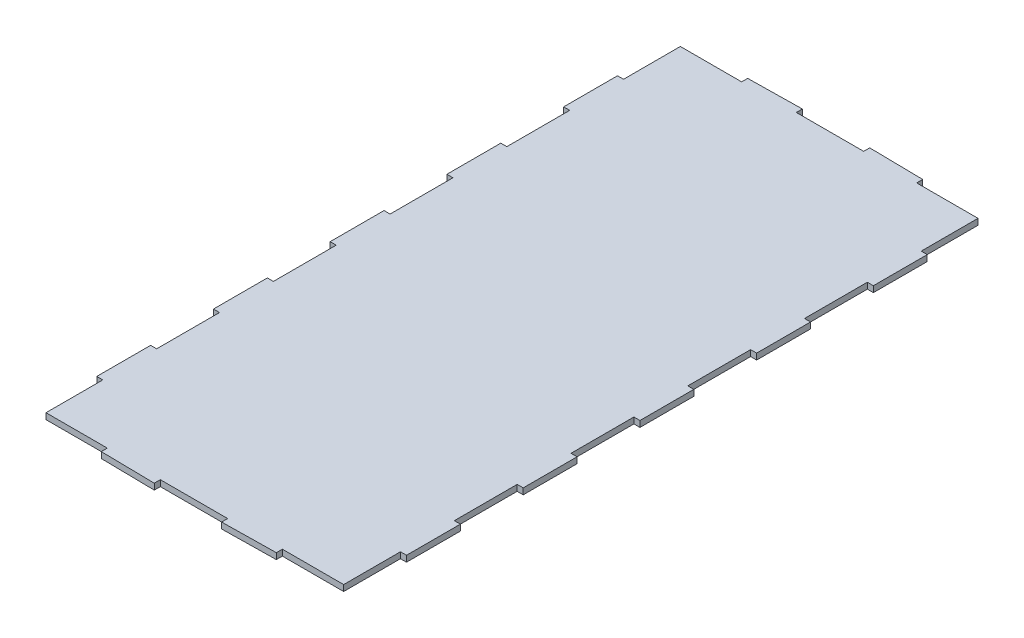
SolidWorks part; units mm, degrees
ref_plane "Front Plane" through (0, 0, 0) normal (0, 0, 1) x (1, 0, 0)
ref_plane "Top Plane" through (0, 0, 0) normal (0, 1, 0) x (1, 0, 0)
ref_plane "Right Plane" through (0, 0, 0) normal (1, 0, 0) x (0, 0, -1)
sketch "Sketch1" plane through (0, 0, 0) normal (0, 1, 0) x (1, 0, 0)
  line L0 (0, 0) -> (0, 299.8917) construction
  line L7 (0, 0) -> (146.05, 0) construction
  line L73 (31.75, 299.8917) -> (-31.75, 299.8917)
  line L102 (31.75, 305.5917) -> (31.75, 299.8917) construction
  line L103 (82.5438, 304.7999) -> (31.75, 305.5917) construction
  line L104 (82.55, 299.0999) -> (82.5438, 304.7999) construction
  line L107 (140.35, 245.5366) -> (146.05, 245.5366)
  line L109 (82.55, 299.0999) -> (82.5438, 304.7999)
  line L110 (82.5438, 304.7999) -> (31.75, 305.5917)
  line L111 (31.75, 305.5917) -> (31.75, 299.8917)
  line L123 (140.35, 245.5366) -> (140.35, 299.0999)
  line L129 (146.05, 245.5366) -> (146.05, 194.7366)
  line L130 (82.55, 299.0999) -> (140.35, 299.0999)
  line L154 (146.05, 194.7366) -> (140.35, 194.7366)
  line L156 (140.35, 194.7366) -> (140.35, 135.47)
  line L157 (140.35, 135.47) -> (146.05, 135.47)
  line L158 (146.05, 135.47) -> (146.05, 84.67)
  line L159 (146.05, 84.67) -> (140.35, 84.67)
  line L160 (140.35, 84.67) -> (140.35, 25.4)
  line L161 (140.35, 25.4) -> (146.05, 25.4)
  line L163 (146.05, 25.4) -> (146.05, -25.4)
  line L165 (-146.05, 25.4) -> (-146.05, -25.4)
  line L166 (-140.35, 245.5366) -> (-140.35, 299.0999)
  line L167 (-140.35, 25.4) -> (-146.05, 25.4)
  line L168 (-140.35, 84.67) -> (-140.35, 25.4)
  line L169 (-146.05, 84.67) -> (-140.35, 84.67)
  line L170 (-146.05, 135.47) -> (-146.05, 84.67)
  line L171 (-140.35, 135.47) -> (-146.05, 135.47)
  line L172 (-140.35, 194.7366) -> (-140.35, 135.47)
  line L173 (-146.05, 194.7366) -> (-140.35, 194.7366)
  line L174 (-146.05, 245.5366) -> (-146.05, 194.7366)
  line L175 (-140.35, 245.5366) -> (-146.05, 245.5366)
  line L176 (-82.55, 299.0999) -> (-82.5438, 304.7999) construction
  line L177 (-82.5438, 304.7999) -> (-31.75, 305.5917) construction
  line L178 (-31.75, 305.5917) -> (-31.75, 299.8917) construction
  line L179 (-82.55, 299.0999) -> (-140.35, 299.0999)
  line L180 (-31.75, 305.5917) -> (-31.75, 299.8917)
  line L181 (-82.5438, 304.7999) -> (-31.75, 305.5917)
  line L182 (-82.55, 299.0999) -> (-82.5438, 304.7999)
  line L186 (-31.75, -305.5917) -> (-31.75, -299.8917) construction
  line L187 (-82.5438, -304.7999) -> (-31.75, -305.5917) construction
  line L188 (-82.55, -299.0999) -> (-82.5438, -304.7999) construction
  line L189 (82.55, -299.0999) -> (82.5438, -304.7999) construction
  line L190 (82.5438, -304.7999) -> (31.75, -305.5917) construction
  line L191 (31.75, -305.5917) -> (31.75, -299.8917) construction
  line L192 (-82.55, -299.0999) -> (-82.5438, -304.7999)
  line L193 (-82.5438, -304.7999) -> (-31.75, -305.5917)
  line L194 (-31.75, -305.5917) -> (-31.75, -299.8917)
  line L195 (-82.55, -299.0999) -> (-140.35, -299.0999)
  line L196 (-140.35, -245.5366) -> (-146.05, -245.5366)
  line L197 (-146.05, -245.5366) -> (-146.05, -194.7366)
  line L198 (-146.05, -194.7366) -> (-140.35, -194.7366)
  line L199 (-140.35, -194.7366) -> (-140.35, -135.47)
  line L200 (-140.35, -135.47) -> (-146.05, -135.47)
  line L201 (-146.05, -135.47) -> (-146.05, -84.67)
  line L202 (-146.05, -84.67) -> (-140.35, -84.67)
  line L203 (-140.35, -84.67) -> (-140.35, -25.4)
  line L204 (-140.35, -25.4) -> (-146.05, -25.4)
  line L205 (-140.35, -245.5366) -> (-140.35, -299.0999)
  line L206 (140.35, -25.4) -> (146.05, -25.4)
  line L207 (140.35, -84.67) -> (140.35, -25.4)
  line L208 (146.05, -84.67) -> (140.35, -84.67)
  line L209 (146.05, -135.47) -> (146.05, -84.67)
  line L210 (140.35, -135.47) -> (146.05, -135.47)
  line L211 (140.35, -194.7366) -> (140.35, -135.47)
  line L212 (146.05, -194.7366) -> (140.35, -194.7366)
  line L213 (82.55, -299.0999) -> (140.35, -299.0999)
  line L214 (146.05, -245.5366) -> (146.05, -194.7366)
  line L215 (140.35, -245.5366) -> (140.35, -299.0999)
  line L216 (31.75, -305.5917) -> (31.75, -299.8917)
  line L217 (82.5438, -304.7999) -> (31.75, -305.5917)
  line L218 (82.55, -299.0999) -> (82.5438, -304.7999)
  line L219 (140.35, -245.5366) -> (146.05, -245.5366)
  line L220 (31.75, -299.8917) -> (-31.75, -299.8917)
  point P30 (-146.05, 0)
  point P65 (0, 299.8917)
  dimension "D2" = 5.7
  dimension "D3" = 50.8
  dimension "D4" = 25.4
  dimension "D5" = 31.75
  dimension "D6" = 59.2666
  dimension "D7" = 50.8
  dimension "D8" = 53.5633
  dimension "D9" = 5.7
  dimension "D10" = 5.7
  dimension "D11" = 50.8
  dimension "D12" = 59.27
  dimension "D13" = 90
  dimension "D16" = 57.8
extrude "Boss-Extrude1" add sketch "Sketch1" along normal blind 5.7
